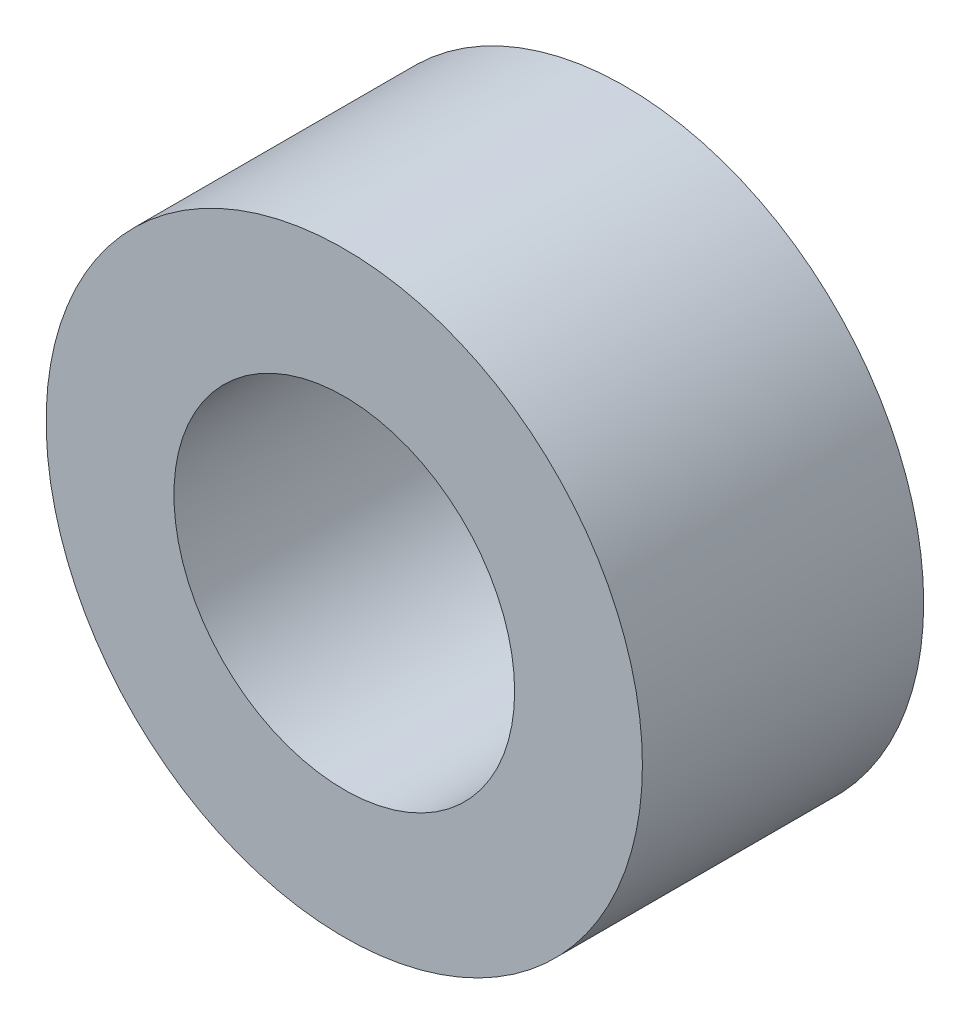
SolidWorks part; units mm, degrees
ref_plane "Front Plane" through (0, 0, 0) normal (0, 0, 1) x (1, 0, 0)
ref_plane "Top Plane" through (0, 0, 0) normal (0, 1, 0) x (1, 0, 0)
ref_plane "Right Plane" through (0, 0, 0) normal (1, 0, 0) x (0, 0, -1)
sketch "Sketch1" plane through (0, 0, 0) normal (0, 0, 1) x (1, 0, 0)
  circle A0 centre (0, 0) radius 6
  circle A1 centre (0, 0) radius 10.5
  point P4 (0, 0)
  point P5 (0, 0)
extrude "Boss-Extrude1" add sketch "Sketch1" along normal blind 9.906 contours A0 | A1
